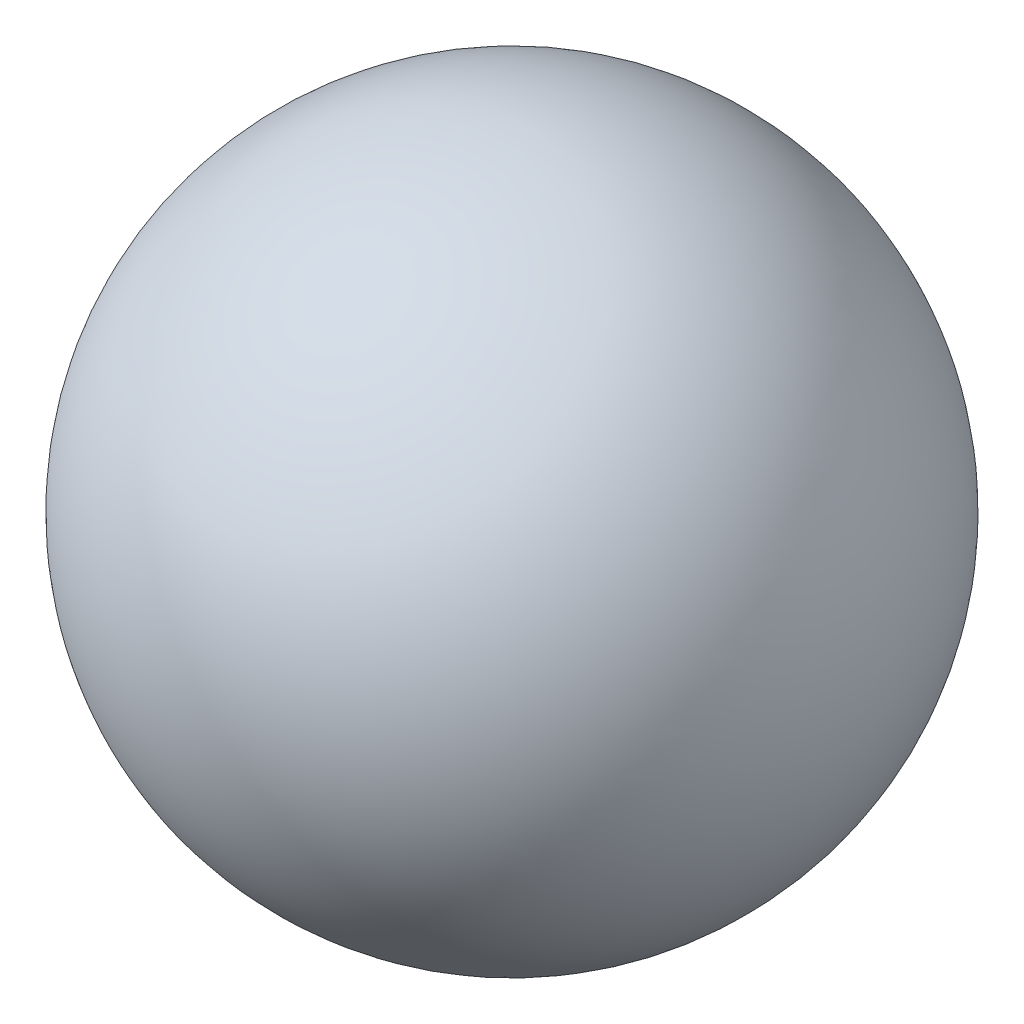
SolidWorks part; units mm, degrees
ref_plane "前视基准面" through (0, 0, 0) normal (0, 0, 1) x (1, 0, 0)
ref_plane "上视基准面" through (0, 0, 0) normal (0, 1, 0) x (1, 0, 0)
ref_plane "右视基准面" through (0, 0, 0) normal (1, 0, 0) x (0, 0, -1)
sketch "草图1" plane through (0, 0, 0) normal (0, 1, 0) x (1, 0, 0)
  line L0 (0, 6.9361) -> (0, -4.0328) construction
  circle A0 centre (0, 0) radius 2
  dimension "D1" = 4
revolve "旋转2" add sketch "草图1" angle 360 about L0
